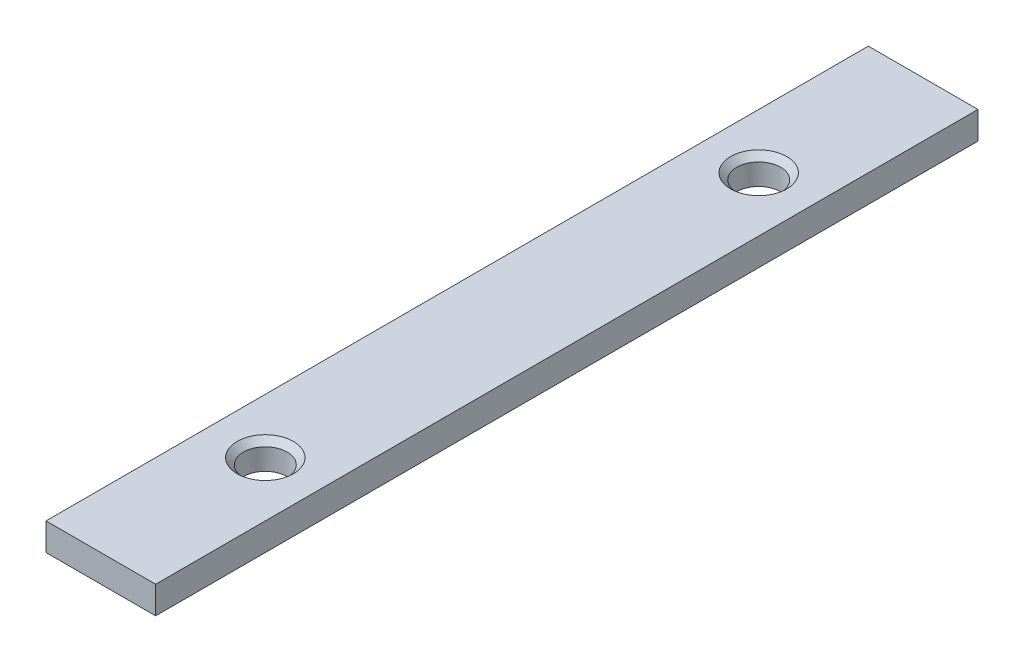
SolidWorks part; units mm, degrees
material "ABS"
ref_plane "Front Plane" through (0, 0, 0) normal (0, 0, 1) x (1, 0, 0)
ref_plane "Top Plane" through (0, 0, 0) normal (0, 1, 0) x (1, 0, 0)
ref_plane "Right Plane" through (0, 0, 0) normal (1, 0, 0) x (0, 0, -1)
sketch "Sketch1" plane through (0, 0, 0) normal (0, 1, 0) x (1, 0, 0)
  line L1 (0, 0) -> (4, 0)
  line L2 (0, 0) -> (0, 30)
  line L3 (0, 30) -> (4, 30)
  line L4 (4, 0) -> (4, 30)
  dimension "D1" = 4
  dimension "D2" = 30
extrude "Boss-Extrude1" add sketch "Sketch1" along normal blind 1
sketch "Sketch2" plane through (0, 1, 0) normal (0, 1, 0) x (1, 0, 0)
  line L0 (4, 0) -> (4, 30) construction
  line L1 (4, 30) -> (0, 30) construction
  line L2 (4, 15) -> (0, 15) construction
  line L3 (0, 30) -> (0, 0) construction
  circle A0 centre (2, 24) radius 1.5
  circle A1 centre (2, 6) radius 1.5
  dimension "D3" = 3
  dimension "D1" = 2
  dimension "D2" = 6
hole_wizard "M2x0.4 Tapped Hole1" positions "3DSketch1" profile "Sketch3" tap size "M2x0.4" standard "ANSI Metric"
sketch3d "3DSketch1"
  point P0 (2, 1, -24)
  point P3 (2, 1, -6)
sketch "Sketch3" plane through (2, 1, -24) normal (1, 0, 0) x (0, 0, 1)
  line L0 (0, 0) -> (0, 11.6807)
  line L1 (0, 11.6807) -> (0.8, 11.2)
  line L2 (0.8, 11.2) -> (0.8, 0.225)
  line L3 (0.8, 0.225) -> (1.025, 0)
  line L5 (1.025, 0) -> (0, 0)
  line L6 (-0.8, 0.225) -> (-1.025, 0) construction
  line L10 (0, 11.6807) -> (-0.8, 11.2) construction
  line L11 (0, -6.35) -> (0, 107.95) construction
  dimension "Tap Drill Dia." = 1.6
  dimension "Tap Drill Depth" = 11.2
  dimension "Near C'Sink Dia." = 2.05
  dimension "Near C'Sink Angle" = 90
  dimension "Drill Angle" = 118
sketch "Sketch8" plane through (0, 0, 0) normal (-1, 0, 0) x (0, 0, 1)
  line L1 (-30, 0) -> (1.6242, 0)
  line L2 (-30, 0) -> (-30, -3.6228)
  line L3 (-30, -3.6228) -> (1.6242, -3.6228)
  line L4 (1.6242, 0) -> (1.6242, -3.6228)
